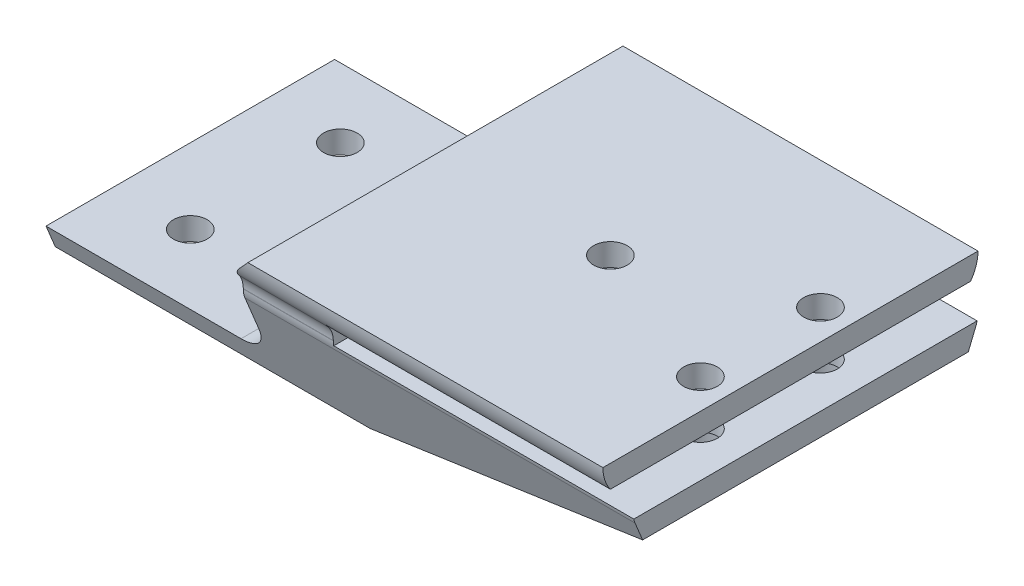
SolidWorks part; units mm, degrees
ref_plane "Front Plane" through (0, 0, 0) normal (0, 0, 1) x (1, 0, 0)
ref_plane "Top Plane" through (0, 0, 0) normal (0, 1, 0) x (1, 0, 0)
ref_plane "Right Plane" through (0, 0, 0) normal (1, 0, 0) x (0, 0, -1)
sketch "Sketch1" plane through (0, 0, 0) normal (0, 0, 1) x (1, 0, 0)
  line L0 (-4.5739, 0) -> (36.4146, 0) construction
  line L1 (0, -3.8426) -> (0, 11.3001) construction
  line L4 (17, -28) -> (17, -21.8403)
  line L5 (-13, -32) -> (13, -32)
  line L6 (-13, -32) -> (-13, -35)
  line L7 (-13, -35) -> (29, -35)
  line L8 (29, -23) -> (29, -20)
  line L9 (29, -20) -> (67, -20)
  line L10 (67, -20) -> (67, -17)
  line L11 (67, -17) -> (19.6723, -17)
  line L12 (29, -35) -> (69, -26)
  line L13 (69, -26) -> (69, -23)
  line L14 (69, -23) -> (29, -23)
  arc A3 (18.4516, -18.3177) -> (19.6723, -17) centre (0, 0) ccw
  arc A4 (18.4516, -18.3177) -> (17, -21.8403) centre (22, -21.8403) ccw
  arc A5 (13, -32) -> (17, -28) centre (13, -28) ccw
  point P22 (-13, -33.5)
  dimension "D6" = 5
  dimension "D9" = 4
  dimension "D11" = 26
  dimension "D1" = 38
  dimension "D2" = 3
  dimension "D3" = 12
  dimension "D4" = 3
  dimension "D5" = 3
  dimension "D7" = 3
  dimension "D8" = 30
  dimension "D10" = 26
  dimension "D12" = 35
  dimension "D13" = 13
  dimension "D14" = 26
  dimension "D15" = 35
  dimension "D16" = 13.1597
  dimension "D17" = 42
  dimension "D18" = 40
extrude "Boss-Extrude1" add sketch "Sketch1" along normal mid plane 60
sketch "Sketch2" plane through (69, 0, 0) normal (1, 0, 0) x (0, 0, -1)
  line L0 (-22.9378, -22.3612) -> (-22.9378, -22.4069)
  line L1 (-30, -23) -> (30, -23) construction
  line L2 (-22.7121, -23.5485) -> (-18, -35)
  line L3 (-30, -35) -> (30, -35) construction
  line L4 (0, -26) -> (0, -48.6994) construction
  line L5 (-30, -26) -> (30, -26) construction
  line L6 (30, -35) -> (18, -35)
  line L7 (-25, -17) -> (-30, -17)
  line L8 (-30, -17) -> (-30, -35)
  line L9 (-30, -35) -> (-18, -35)
  line L10 (30, -17) -> (30, -35)
  line L11 (25, -17) -> (30, -17)
  line L12 (22.7121, -23.5485) -> (18, -35)
  line L13 (22.9378, -22.3612) -> (22.9378, -22.4069)
  arc A0 (22.9378, -22.4069) -> (22.7121, -23.5485) centre (19.9378, -22.4069) cw
  arc A1 (-25, -17) -> (-23.7111, -20.3507) centre (-20, -17) ccw
  arc A2 (-23.7111, -20.3507) -> (-22.9378, -22.3612) centre (-25.9378, -22.3612) cw
  arc A3 (-22.9378, -22.4069) -> (-22.7121, -23.5485) centre (-19.9378, -22.4069) ccw
  arc A4 (23.7111, -20.3507) -> (22.9378, -22.3612) centre (25.9378, -22.3612) ccw
  arc A5 (25, -17) -> (23.7111, -20.3507) centre (20, -17) cw
  point P16 (0, -37.3497)
  point P24 (-22.9378, -23)
  point P37 (22.9378, -23)
  dimension "D1" = 5
  dimension "D3" = 3
  dimension "D4" = 3
  dimension "D2" = 18
  dimension "D5" = 20
extrude "Cut-Extrude1" cut sketch "Sketch2" against normal up to surface (82 mm away) up to face at (-13, -33.5, 0)
sketch "Sketch3" plane through (0, -35, 0) normal (0, -1, 0) x (-1, 0, 0)
  line L0 (13, -18) -> (13, 18) construction
  line L3 (0, 0) -> (-78.1283, 0) construction
  circle A0 centre (3, -10) radius 2.25
  circle A1 centre (3, 10) radius 2.25
  dimension "D1" = 4.5
  dimension "D2" = 10
  dimension "D3" = 10
extrude "Cut-Extrude2" cut sketch "Sketch3" against normal blind 60
hole_wizard "Hole2" positions "Sketch8" profile "Sketch9" legacy end condition through all
sketch "Sketch8" plane through (0, -35, 0) normal (0, -1, 0) x (-1, 0, 0)
  line L0 (0, 0) -> (-82.992, 0) construction
  line L3 (-29, 23.7111) -> (-29, 22.9378) construction
  point P0 (-63, 8)
  point P2 (-63, -8)
  point P14 (-43, 0)
  dimension "D1" = 8
  dimension "D2" = 8
  dimension "D3" = 34
  dimension "D4" = 20
sketch "Sketch9" plane through (63, -35, -8) normal (1, 0, 0) x (0, 0, -1)
  line L0 (0, 0) -> (0, 18)
  line L1 (0, 18) -> (2.25, 18)
  line L2 (2.25, 18) -> (2.25, 10)
  line L3 (2.25, 10) -> (3, 10)
  line L4 (3, 10) -> (3, 0)
  line L5 (3, 0) -> (0, 0)
  line L6 (0, 110) -> (0, -10) construction
  dimension "Diameter" = 4.5
  dimension "Depth" = 18
  dimension "C-Bore Diameter" = 6
  dimension "C-Bore Depth" = 10
